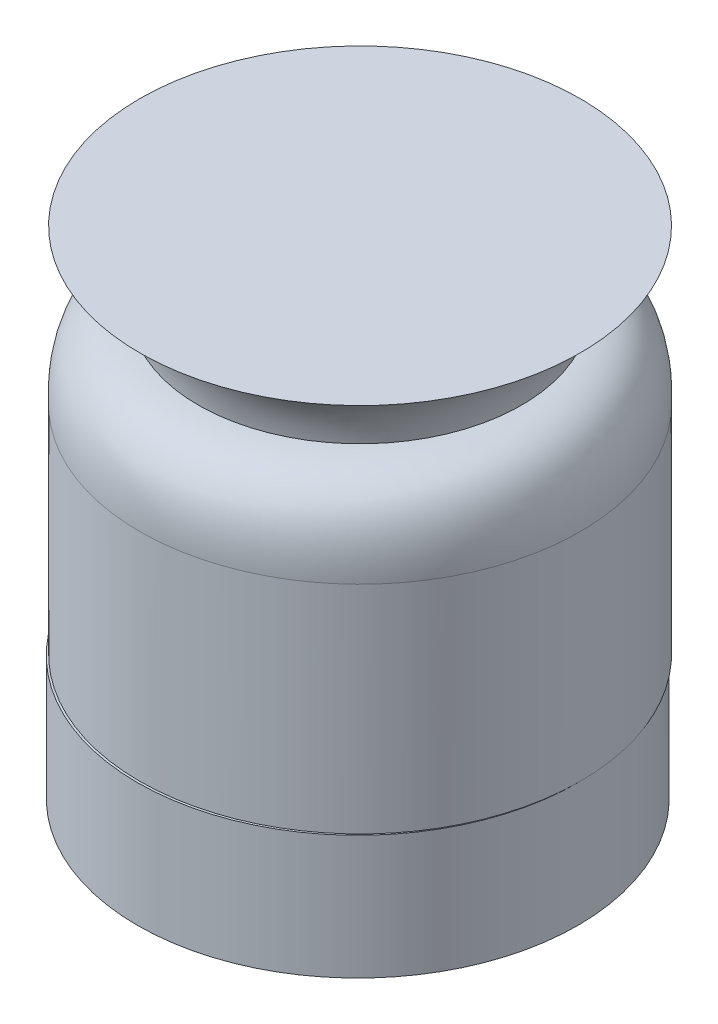
SolidWorks part; units mm, degrees
material "Polybutadiene (PB)"
ref_plane "Front Plane" through (0, 0, 0) normal (0, 0, 1) x (1, 0, 0)
ref_plane "Top Plane" through (0, 0, 0) normal (0, 1, 0) x (1, 0, 0)
ref_plane "Right Plane" through (0, 0, 0) normal (1, 0, 0) x (0, 0, -1)
sketch "Sketch1" plane through (0, 0, 0) normal (0, 1, 0) x (1, 0, 0)
  line L0 (9.525, -1.905) -> (9.525, 4.445)
  line L1 (9.525, 4.445) -> (-6.985, 4.445)
  line L2 (-9.525, 1.905) -> (-9.525, -4.445)
  line L3 (-9.525, -4.445) -> (6.985, -4.445)
  arc A0 (-6.985, 4.445) -> (-9.525, 1.905) centre (-6.985, 1.905) ccw
  arc A1 (6.985, -4.445) -> (9.525, -1.905) centre (6.985, -1.905) ccw
sketch "Sketch2" plane through (0, 0, 0) normal (0, 0, 1) x (-1, 0, 0)
  line L0 (0, 0) -> (0, -38.1)
  line L1 (0, -38.1) -> (-76.2, -38.1)
  line L2 (-76.2, -38.1) -> (-76.2, -203.2)
  dimension "D1" = 38.1
  dimension "D2" = 76.2
  dimension "D3" = 165.1
sweep "Sweep2" add profiles "Sketch1" path "Sketch2"
ref_plane "Plane1" through (0, -15.875, 0) normal (0, 1, 0) x (1, 0, 0)
sketch "Sketch3" plane through (0, -15.875, 0) normal (0, 1, 0) x (1, 0, 0)
  line L0 (9.525, 4.445) -> (9.525, 47.004)
  line L2 (-85.475, 47.004) -> (-85.475, -1.905)
  line L3 (-82.935, -4.445) -> (-9.525, -4.445)
  line L4 (-9.525, -4.445) -> (6.985, -4.445)
  line L5 (-9.525, 1.905) -> (-9.525, -4.445)
  line L6 (9.525, 4.445) -> (-6.985, 4.445)
  line L7 (9.525, -1.905) -> (9.525, 4.445)
  line L8 (-9.525, -4.445) -> (6.985, -4.445)
  line L11 (9.525, -1.905) -> (9.525, 4.445)
  arc A0 (-85.475, -1.905) -> (-82.935, -4.445) centre (-82.935, -1.905) ccw
  arc A1 (9.525, 47.004) -> (-85.475, 47.004) centre (-37.975, 47.004) ccw
  arc A2 (6.985, -4.445) -> (9.525, -1.905) centre (6.985, -1.905) ccw
  arc A3 (-6.985, 4.445) -> (-9.525, 1.905) centre (-6.985, 1.905) ccw
  arc A4 (6.985, -4.445) -> (9.525, -1.905) centre (6.985, -1.905) ccw
  dimension "D2" = 2.54
  dimension "D3" = 47.5
  dimension "D1" = 0
extrude "Boss-Extrude1" add sketch "Sketch3" along normal blind 26.67
ref_plane "Plane2" through (-37.975, 0, 0) normal (-1, 0, 0) x (0, 0, 1)
mirror "Mirror1" about plane through (-37.975, 0, 0) normal (-1, 0, 0) of "Sweep2"
sketch "Sketch4" plane through (0, 10.795, 0) normal (0, 1, 0) x (1, 0, 0)
  circle A0 centre (-37.975, 47.004) radius 29.9197
extrude "Boss-Extrude2" add sketch "Sketch4" along normal blind 6
fillet "Fillet1" radius 2 2 edges at (-37.975, 10.795, -17.0844) (-37.975, 16.795, -17.0844)
fillet "Fillet2" [suppressed] radius 12
fillet "Fillet3" radius 12 7 edges at (-123.575, 28.575, 1.905) (-84.7311, 29.3189, 3.7011) (-85.475, 28.575, -1.27) (9.525, 28.575, -1.27) (8.7811, 29.3189, 3.7011) (47.625, 28.575, 1.905) (-85.475, 6.35, 1.905)
fillet "Fillet4" radius 12 4 edges at (-143.3689, 46.8811, -3.7011) (67.4189, 46.8811, -3.7011) (-142.625, 47.625, 1.27) (66.675, 47.625, 1.27)
sketch "Sketch5" plane through (0, 0, -4.445) normal (0, 0, -1) x (-1, 0, 0)
  line L1 (-127.5162, 10.795) -> (220.6797, 10.795)
  line L2 (-127.5162, 10.795) -> (-127.5162, 217.3279)
  line L3 (-127.5162, 217.3279) -> (220.6797, 217.3279)
  line L4 (220.6797, 10.795) -> (220.6797, 217.3279)
extrude "Cut-Extrude1" cut sketch "Sketch5" against normal through all both and the other way through all
sketch "Sketch6" plane through (0, 10.795, 0) normal (0, 1, 0) x (1, 0, 0)
  line L3 (-85.475, 47.004) -> (-85.475, -1.905)
  line L4 (-82.935, -4.445) -> (6.985, -4.445)
  line L5 (9.525, -1.905) -> (9.525, 47.004)
  line L6 (-85.475, 47.004) -> (-85.475, -1.905)
  line L7 (-82.935, -4.445) -> (6.985, -4.445)
  line L8 (9.525, -1.905) -> (9.525, 47.004)
  arc A3 (-85.475, -1.905) -> (-82.935, -4.445) centre (-82.935, -1.905) ccw
  arc A4 (6.985, -4.445) -> (9.525, -1.905) centre (6.985, -1.905) ccw
  arc A5 (9.525, 47.004) -> (-85.475, 47.004) centre (-37.975, 47.004) ccw
  arc A6 (-85.475, -1.905) -> (-82.935, -4.445) centre (-82.935, -1.905) ccw
  arc A7 (6.985, -4.445) -> (9.525, -1.905) centre (6.985, -1.905) ccw
  arc A8 (9.525, 47.004) -> (-85.475, 47.004) centre (-37.975, 47.004) ccw
  dimension "D1" = 0
sketch "Sketch7" plane through (0, -15.875, 0) normal (0, -1, 0) x (1, 0, 0)
  circle A0 centre (-37.975, -47.004) radius 47.5
  circle A1 centre (-37.975, -47.004) radius 81.9114
extrude "Cut-Extrude2" cut sketch "Sketch7" against normal through all both contours A0 | A1
ref_plane "Plane3" through (0, 0, -47.5) normal (0, 0, 1) x (1, 0, 0)
sketch "Sketch9" plane through (0, 0, -47.5) normal (0, 0, 1) x (1, 0, 0)
  line L0 (-37.975, 10.795) -> (-37.975, 84.2008) construction
  line L1 (9.525, 10.795) -> (-85.475, 10.795) construction
  line L2 (9.525, 10.795) -> (9.525, 57.4269)
  line L4 (9.525, 90.795) -> (-37.975, 90.795)
  line L5 (-37.975, 90.795) -> (-37.975, 10.795)
  line L6 (-37.975, 10.795) -> (9.525, 10.795)
  line L7 (-37.975, 10.795) -> (-37.975, -45.4041) construction
  spline S0 degree 2 poles (9.525, 57.4269) (10.2923, 74.3611) (-3.0982, 74.7349) knots 0 0 0 1 1 1
  spline S1 degree 2 poles (-3.0982, 74.7349) (-1.4362, 87.7642) (9.525, 90.795) knots 0 0 0 1 1 1
  point P10 (9.525, 112.4905)
  point P11 (-1.2103, 78.8798)
  point P15 (0, 0)
  point P16 (0, 0)
  point P17 (0, 81.8322)
  point P18 (0, 79.1481)
  point P19 (-3.0982, 74.7349)
  dimension "D1" = 80
revolve "Revolve1" add sketch "Sketch9" angle 360 about L7
